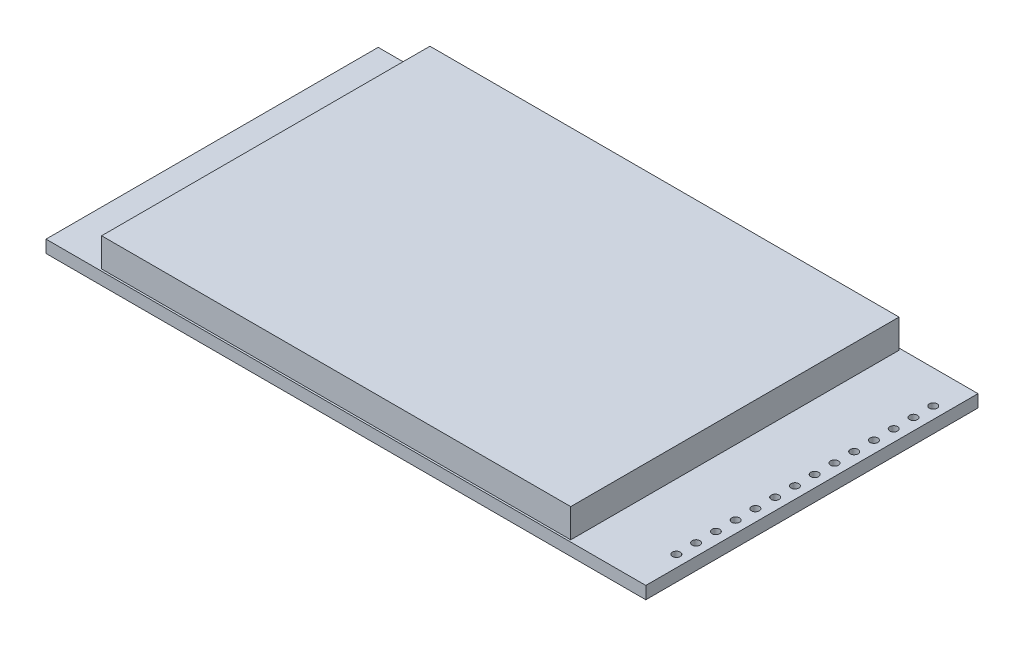
SolidWorks part; units mm, degrees
material "ABS"
ref_plane "Front" through (0, 0, 0) normal (0, 0, 1) x (1, 0, 0)
ref_plane "Top" through (0, 0, 0) normal (0, 1, 0) x (1, 0, 0)
ref_plane "Right" through (0, 0, 0) normal (1, 0, 0) x (0, 0, -1)
sketch "Croquis1" plane through (0, 0, 0) normal (0, 1, 0) x (1, 0, 0)
  line L1 (38.55, -21.35) -> (-38.55, -21.35)
  line L2 (38.55, -21.35) -> (38.55, 21.35)
  line L3 (38.55, 21.35) -> (-38.55, 21.35)
  line L4 (-38.55, -21.35) -> (-38.55, 21.35)
  line L5 (38.55, -21.35) -> (-38.55, 21.35) construction
  line L6 (38.55, 21.35) -> (-38.55, -21.35) construction
  point P0 (0, 0)
  dimension "D1" = 77.1
  dimension "D2" = 42.7
extrude "Saliente-Extruir1" add sketch "Croquis1" along normal blind 1.6
sketch "Croquis2" plane through (0, 1.6, 0) normal (0, 1, 0) x (1, 0, 0)
  line L0 (-38.55, 21.35) -> (-38.55, -21.35) construction
  line L1 (28.65, -21.1) -> (-31.65, -21.1)
  line L2 (28.65, -21.1) -> (28.65, 21.1)
  line L3 (28.65, 21.1) -> (-31.65, 21.1)
  line L4 (-31.65, -21.1) -> (-31.65, 21.1)
  line L5 (28.65, -21.1) -> (-31.65, 21.1) construction
  line L6 (28.65, 21.1) -> (-31.65, -21.1) construction
  line L8 (38.55, -21.35) -> (38.55, 21.35) construction
  point P0 (-1.5, 0)
  dimension "D1" = 6.9
  dimension "D2" = 42.2
  dimension "D3" = 9.9
extrude "Saliente-Extruir2" add sketch "Croquis2" along normal offset from surface (3.7 mm away) 5.3 up to face at (0, 0, 0)
sketch "Croquis3" plane through (0, 1.6, 0) normal (0, 1, 0) x (1, 0, 0)
  line L0 (38.55, -21.35) -> (38.55, 21.35) construction
  circle A0 centre (37.05, -15.9232) radius 0.5
  circle A1 centre (37.05, -13.3832) radius 0.5
  circle A2 centre (37.05, -10.8432) radius 0.5
  circle A3 centre (37.05, -8.3032) radius 0.5
  circle A4 centre (37.05, -5.7632) radius 0.5
  circle A5 centre (37.05, -3.2232) radius 0.5
  circle A6 centre (37.05, -0.6832) radius 0.5
  circle A7 centre (37.05, 1.8568) radius 0.5
  circle A8 centre (37.05, 4.3968) radius 0.5
  circle A9 centre (37.05, 6.9368) radius 0.5
  circle A10 centre (37.05, 9.4768) radius 0.5
  circle A11 centre (37.05, 12.0168) radius 0.5
  circle A12 centre (37.05, 14.5568) radius 0.5
  circle A13 centre (37.05, 17.0968) radius 0.5
  dimension "D1" = 1
  dimension "D2" = 1.5
  dimension "D3" = 14
extrude "Cortar-Extruir1" cut sketch "Croquis3" against normal up to next
sketch "Croquis4" [suppressed] plane through (0, 0, 0) normal (0, -1, 0) x (1, 0, 0)
  line L0 (38.55, 21.35) -> (38.55, -21.35) construction
  line L1 (31.65, -18.3) -> (-35.85, -18.3) construction
  line L2 (31.65, -18.3) -> (31.65, 18.3) construction
  line L3 (31.65, 18.3) -> (-35.85, 18.3) construction
  line L4 (-35.85, -18.3) -> (-35.85, 18.3) construction
  line L5 (31.65, -18.3) -> (-35.85, 18.3) construction
  line L6 (31.65, 18.3) -> (-35.85, -18.3) construction
  circle A0 centre (-35.85, 18.3) radius 1.5
  circle A1 centre (31.65, 18.3) radius 1.5
  circle A2 centre (31.65, -18.3) radius 1.5
  circle A3 centre (-35.85, -18.3) radius 1.5
  point P0 (-2.1, 0)
  dimension "D1" = 3
  dimension "D2" = 67.5
  dimension "D3" = 36.6
  dimension "D4" = 6.9
extrude "Cortar-Extruir2" [suppressed] cut sketch "Croquis4" against normal up to next
